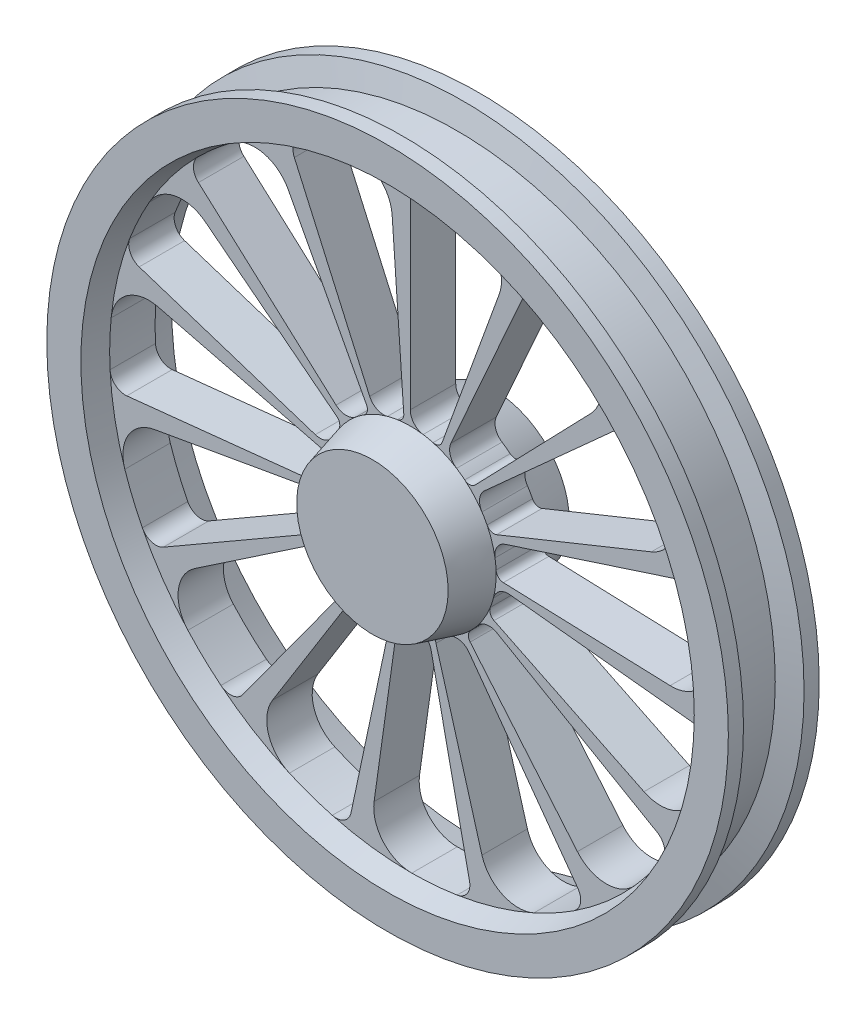
SolidWorks part; units mm, degrees
material "1060 Alloy"
ref_plane "Front Plane" through (0, 0, 0) normal (0, 0, 1) x (1, 0, 0)
ref_plane "Top Plane" through (0, 0, 0) normal (0, 1, 0) x (1, 0, 0)
ref_plane "Right Plane" through (0, 0, 0) normal (1, 0, 0) x (0, 0, -1)
sketch "Sketch1" plane through (0, 0, 0) normal (1, 0, 0) x (0, 0, -1)
  line L0 (-80, 0) -> (80, 0) construction
  line L1 (-80, 0) -> (-80, 100)
  line L2 (-80, 100) -> (-30, 113.3975)
  line L3 (-30, 113.3975) -> (-30, 396.9615)
  line L4 (-30, 396.9615) -> (-60, 405)
  line L5 (-60, 405) -> (-60, 450)
  line L6 (-60, 450) -> (-40, 450)
  line L7 (0, 0) -> (0, 563.296) construction
  line L8 (-40, 450) -> (-31.9615, 420)
  line L9 (-31.9615, 420) -> (31.9615, 420)
  line L10 (-80, 0) -> (80, 0)
  line L11 (80, 0) -> (80, 100)
  line L12 (80, 100) -> (30, 113.3975)
  line L13 (30, 113.3975) -> (30, 396.9615)
  line L14 (30, 396.9615) -> (60, 405)
  line L15 (60, 405) -> (60, 450)
  line L16 (60, 450) -> (40, 450)
  line L17 (40, 450) -> (31.9615, 420)
  point P3 (-63.6069, 444.241)
  point P4 (0, 0)
  point P8 (-10.5862, 373.0495)
  point P15 (-5.2816, 398.4864)
  point P16 (-24.3964, 396.3697)
  point P17 (-44.6855, 444.7868)
  point P25 (0, 420)
  dimension "D3" = 15
  dimension "D4" = 100
  dimension "D2" = 450
  dimension "D5" = 30
  dimension "D6" = 120
  dimension "D7" = 20
  dimension "D8" = 15
  dimension "D9" = 15
  dimension "D10" = 60
  dimension "D11" = 45
  dimension "D12" = 160
revolve "Revolve1" add sketch "Sketch1" angle 360 about L10
sketch "Sketch3" plane through (0, 0, 30) normal (0, 0, 1) x (1, 0, 0)
  line L0 (0, 131.8897) -> (0, 376.4306)
  line L1 (42.0656, 115.5743) -> (117.4292, 322.634)
  line L2 (53.6444, 120.4872) -> (153.1081, 343.8865)
  line L3 (85.4371, 88.4728) -> (238.5039, 246.9781)
  line L4 (98.0131, 88.2514) -> (279.7424, 251.8812)
  line L5 (114.0358, 46.0735) -> (318.3392, 128.6174)
  line L6 (125.4345, 40.7561) -> (358.0068, 116.3235)
  line L7 (122.9167, -4.2923) -> (343.1308, -11.9824)
  line L8 (131.1672, -13.7862) -> (374.3685, -39.3477)
  line L9 (110.5441, -53.916) -> (308.5919, -150.5103)
  line L10 (114.2198, -65.9448) -> (325.9985, -188.2153)
  line L11 (79.0575, -94.217) -> (220.6946, -263.0136)
  line L12 (77.5228, -106.701) -> (221.2604, -304.5387)
  line L13 (33.9011, -118.2271) -> (94.6373, -330.0395)
  line L14 (27.4214, -129.0076) -> (78.2643, -368.2047)
  line L15 (-17.1171, -121.7947) -> (-47.7837, -339.9986)
  line L16 (-27.4214, -129.0076) -> (-78.2643, -368.2047)
  line L17 (-65.1756, -104.3028) -> (-181.9424, -291.1688)
  line L18 (-77.5228, -106.701) -> (-221.2604, -304.5387)
  line L19 (-101.9647, -68.776) -> (-284.6417, -191.9932)
  line L20 (-114.2198, -65.9448) -> (-325.9985, -188.2153)
  line L21 (-121.1231, -21.3573) -> (-338.1238, -59.6204)
  line L22 (-131.1672, -13.7862) -> (-374.3685, -39.3477)
  line L23 (-119.3382, 29.7544) -> (-333.1413, 83.0614)
  line L24 (-125.4345, 40.7561) -> (-358.0068, 116.3235)
  line L25 (-96.9187, 75.7212) -> (-270.5555, 211.3812)
  line L26 (-98.0131, 88.2514) -> (-279.7424, 251.8812)
  line L27 (-57.7411, 108.5951) -> (-161.1883, 303.1512)
  line L28 (-53.6444, 120.4872) -> (-153.1081, 343.8865)
  line L29 (-8.5795, 122.692) -> (-23.9502, 342.5036)
  circle A0 centre (0, 0) radius 113.3975 construction
  circle A1 centre (0, 0) radius 396.9615 construction
  arc A2 (30.0212, 109.3513) -> (17.0014, 112.1157) centre (0, 0) ccw
  arc A3 (80.5962, 388.6936) -> (21.0611, 396.4024) centre (0, 0) ccw
  arc A4 (0, 131.8897) -> (17.0014, 112.1157) centre (20, 131.8897) ccw
  arc A5 (0, 376.4306) -> (21.0611, 396.4024) centre (20, 376.4306) cw
  arc A6 (117.4292, 322.634) -> (80.5962, 388.6936) centre (70.4445, 339.735) ccw
  arc A7 (42.0656, 115.5743) -> (30.0212, 109.3513) centre (32.6687, 118.9945) cw
  arc A8 (71.903, 87.6867) -> (61.1332, 95.5077) centre (0, 0) ccw
  arc A9 (85.4371, 88.4728) -> (71.903, 87.6867) centre (78.2437, 95.4193) cw
  arc A10 (53.6444, 120.4872) -> (61.1332, 95.5077) centre (71.9153, 112.3525) ccw
  arc A11 (153.1081, 343.8865) -> (180.4717, 353.5653) centre (171.379, 335.7517) cw
  arc A12 (231.7242, 322.3078) -> (180.4717, 353.5653) centre (0, 0) ccw
  arc A13 (238.5039, 246.9781) -> (231.7242, 322.3078) centre (202.537, 281.711) ccw
  arc A14 (101.352, 50.8602) -> (94.6944, 62.3855) centre (0, 0) ccw
  arc A15 (114.0358, 46.0735) -> (101.352, 50.8602) centre (110.2898, 55.3453) cw
  arc A16 (98.0131, 88.2514) -> (94.6944, 62.3855) centre (111.3957, 73.3885) ccw
  arc A17 (279.7424, 251.8812) -> (308.677, 249.5935) centre (293.1251, 237.0183) cw
  arc A18 (342.785, 200.1922) -> (308.677, 249.5935) centre (0, 0) ccw
  arc A19 (318.3392, 128.6174) -> (342.785, 200.1922) centre (299.6089, 174.9766) ccw
  arc A20 (113.2763, 5.2395) -> (111.8821, 18.4763) centre (0, 0) ccw
  arc A21 (122.9167, -4.2923) -> (113.2763, 5.2395) centre (123.2657, 5.7016) cw
  arc A22 (125.4345, 40.7561) -> (111.8821, 18.4763) centre (131.6149, 21.735) ccw
  arc A23 (358.0068, 116.3235) -> (383.5094, 102.4648) centre (364.1871, 97.3023) cw
  arc A24 (394.5752, 43.4614) -> (383.5094, 102.4648) centre (0, 0) ccw
  arc A25 (343.1308, -11.9824) -> (394.5752, 43.4614) centre (344.8757, 37.9872) ccw
  arc A26 (105.6142, -41.2871) -> (109.7244, -28.6276) centre (0, 0) ccw
  arc A27 (110.5441, -53.916) -> (105.6142, -41.2871) centre (114.9278, -44.928) cw
  arc A28 (131.1672, -13.7862) -> (109.7244, -28.6276) centre (129.0766, -33.6767) ccw
  arc A29 (374.3685, -39.3477) -> (392.0294, -62.3811) centre (372.2779, -59.2381) cw
  arc A30 (378.1397, -120.7842) -> (392.0294, -62.3811) centre (0, 0) ccw
  arc A31 (308.5919, -150.5103) -> (378.1397, -120.7842) centre (330.5104, -105.5706) ccw
  arc A32 (79.6904, -80.6748) -> (88.5943, -70.7815) centre (0, 0) ccw
  arc A33 (79.0575, -94.217) -> (79.6904, -80.6748) centre (86.7179, -87.7892) cw
  arc A34 (114.2198, -65.9448) -> (88.5943, -70.7815) centre (104.2198, -83.2653) ccw
  arc A35 (325.9985, -188.2153) -> (332.764, -216.4407) centre (315.9985, -205.5358) cw
  arc A36 (296.3204, -264.1451) -> (332.764, -216.4407) centre (0, 0) ccw
  arc A37 (220.6946, -263.0136) -> (296.3204, -264.1451) centre (258.9969, -230.8743) ccw
  arc A38 (39.9874, -106.1131) -> (52.1455, -100.6967) centre (0, 0) ccw
  arc A39 (33.9011, -118.2271) -> (39.9874, -106.1131) centre (43.5137, -115.4707) cw
  arc A40 (77.5228, -106.701) -> (52.1455, -100.6967) centre (61.3425, -118.4567) ccw
  arc A41 (221.2604, -304.5387) -> (215.9607, -333.0757) centre (205.08, -316.2945) cw
  arc A42 (163.2647, -361.833) -> (215.9607, -333.0757) centre (0, 0) ccw
  arc A43 (94.6373, -330.0395) -> (163.2647, -361.833) centre (142.7004, -316.2576) ccw
  arc A44 (-6.6298, -113.2035) -> (6.6802, -113.2005) centre (0, 0) ccw
  arc A45 (-17.1171, -121.7947) -> (-6.6298, -113.2035) centre (-7.2144, -123.1864) cw
  arc A46 (27.4214, -129.0076) -> (6.6802, -113.2005) centre (7.8585, -133.1658) ccw
  arc A47 (78.2643, -368.2047) -> (61.8158, -392.1189) centre (58.7014, -372.3629) cw
  arc A48 (1.979, -396.9566) -> (61.8158, -392.1189) centre (0, 0) ccw
  arc A49 (-47.7837, -339.9986) -> (1.979, -396.9566) centre (1.7297, -346.9572) ccw
  arc A50 (-52.1006, -100.72) -> (-39.9401, -106.1309) centre (0, 0) ccw
  arc A51 (-65.1756, -104.3028) -> (-52.1006, -100.72) centre (-56.6951, -109.602) cw
  arc A52 (-27.4214, -129.0076) -> (-39.9401, -106.1309) centre (-46.9844, -124.8493) ccw
  arc A53 (-78.2643, -368.2047) -> (-103.0176, -383.3612) centre (-97.8273, -364.0464) cw
  arc A54 (-159.6489, -363.4428) -> (-103.0176, -383.3612) centre (0, 0) ccw
  arc A55 (-181.9424, -291.1688) -> (-159.6489, -363.4428) centre (-139.54, -317.6647) ccw
  arc A56 (-88.5628, -70.821) -> (-79.6544, -80.7103) centre (0, 0) ccw
  arc A57 (-101.9647, -68.776) -> (-88.5628, -70.821) centre (-96.3727, -77.0664) cw
  arc A58 (-77.5228, -106.701) -> (-79.6544, -80.7103) centre (-93.7031, -94.9453) ccw
  arc A59 (-221.2604, -304.5387) -> (-250.0383, -308.3169) centre (-237.4407, -292.783) cw
  arc A60 (-293.672, -267.0865) -> (-250.0383, -308.3169) centre (0, 0) ccw
  arc A61 (-284.6417, -191.9932) -> (-293.672, -267.0865) centre (-256.682, -233.4451) ccw
  arc A62 (-109.7116, -28.6765) -> (-105.5958, -41.3342) centre (0, 0) ccw
  arc A63 (-121.1231, -21.3573) -> (-109.7116, -28.6765) centre (-119.3866, -31.2053) cw
  arc A64 (-114.2198, -65.9448) -> (-105.5958, -41.3342) centre (-124.2198, -48.6243) ccw
  arc A65 (-325.9985, -188.2153) -> (-353.8251, -179.9617) centre (-335.9985, -170.8948) cw
  arc A66 (-376.9166, -124.5485) -> (-353.8251, -179.9617) centre (0, 0) ccw
  arc A67 (-338.1238, -59.6204) -> (-376.9166, -124.5485) centre (-329.4414, -108.8607) ccw
  arc A68 (-111.8903, 18.4265) -> (-113.2787, 5.189) centre (0, 0) ccw
  arc A69 (-119.3382, 29.7544) -> (-111.8903, 18.4265) centre (-121.7574, 20.0514) cw
  arc A70 (-131.1672, -13.7862) -> (-113.2787, 5.189) centre (-133.2577, 6.1042) ccw
  arc A71 (-374.3685, -39.3477) -> (-396.4324, -20.4896) centre (-376.459, -19.4573) cw
  arc A72 (-394.9889, 39.5251) -> (-396.4324, -20.4896) centre (0, 0) ccw
  arc A73 (-333.1413, 83.0614) -> (-394.9889, 39.5251) centre (-345.2373, 34.5467) ccw
  arc A74 (-94.7222, 62.3433) -> (-101.3747, 50.815) centre (0, 0) ccw
  arc A75 (-96.9187, 75.7212) -> (-94.7222, 62.3433) centre (-103.0753, 67.8411) cw
  arc A76 (-125.4345, 40.7561) -> (-101.3747, 50.815) centre (-119.2542, 59.7773) ccw
  arc A77 (-358.0068, 116.3235) -> (-370.4929, 142.5254) centre (-351.8264, 135.3446) cw
  arc A78 (-344.764, 196.7644) -> (-370.4929, 142.5254) centre (0, 0) ccw
  arc A79 (-270.5555, 211.3812) -> (-344.764, 196.7644) centre (-301.3386, 171.9806) ccw
  arc A80 (-61.1757, 95.4804) -> (-71.942, 87.6546) centre (0, 0) ccw
  arc A81 (-57.7411, 108.5951) -> (-61.1757, 95.4804) centre (-66.5705, 103.9004) cw
  arc A82 (-98.0131, 88.2514) -> (-71.942, 87.6546) centre (-84.6305, 103.1143) ccw
  arc A83 (-279.7424, 251.8812) -> (-280.4918, 280.8965) centre (-266.3598, 266.7441) cw
  arc A84 (-234.9263, 319.9814) -> (-280.4918, 280.8965) centre (0, 0) ccw
  arc A85 (-161.1883, 303.1512) -> (-234.9263, 319.9814) centre (-205.3357, 279.6776) ccw
  arc A86 (-17.0514, 112.1081) -> (-30.07, 109.3379) centre (0, 0) ccw
  arc A87 (-8.5795, 122.692) -> (-17.0514, 112.1081) centre (-18.5551, 121.9944) cw
  arc A88 (-53.6444, 120.4872) -> (-30.07, 109.3379) centre (-35.3734, 128.6219) ccw
  arc A89 (-153.1081, 343.8865) -> (-141.9911, 370.698) centre (-134.8372, 352.0212) cw
  arc A90 (-84.4677, 387.8707) -> (-141.9911, 370.698) centre (0, 0) ccw
  arc A91 (-23.9502, 342.5036) -> (-84.4677, 387.8707) centre (-73.8284, 339.0157) ccw
  point P10 (0, 113.3975)
  point P13 (0, 396.9615)
  point P188 (0, 0)
  dimension "D2" = 20
  dimension "D3" = 50
  dimension "D4" = 10
  dimension "D1" = 20
  dimension "D5" = 15
extrude "Cut-Extrude1" cut sketch "Sketch3" against normal through all both and the other way through all
equation "\"A\"= 120"
equation "\"B\"= 900"
equation "\"D2@Sketch1\"=\"B\"/2"
equation "\"D6@Sketch1\"=\"A\""
equation "\"D12@Sketch1\"=\"A\"+40"
